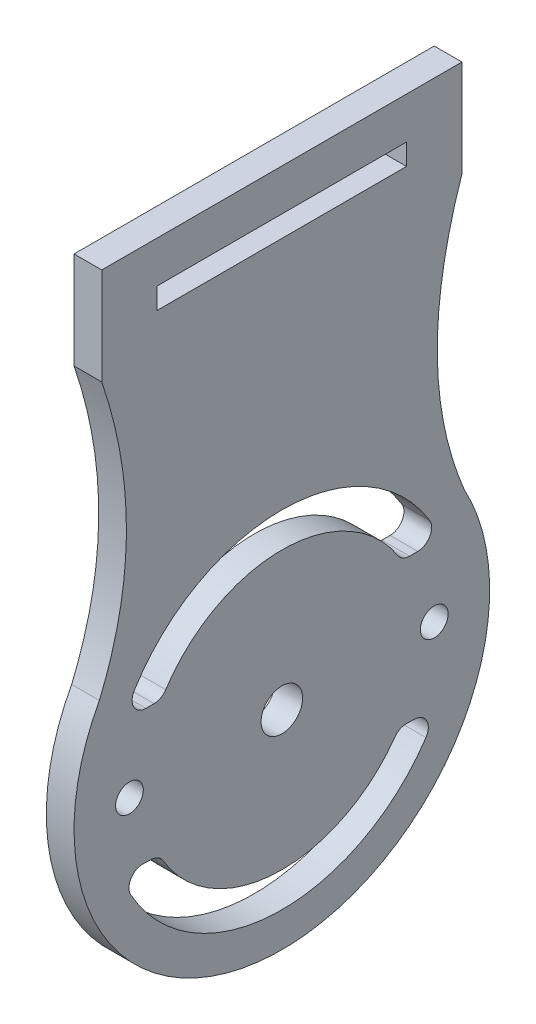
SolidWorks part; units mm, degrees
material "Fibra de Vidro S"
ref_plane "Plano frontal" through (0, 0, 0) normal (0, 0, 1) x (1, 0, 0)
ref_plane "Plano superior" through (0, 0, 0) normal (0, 1, 0) x (1, 0, 0)
ref_plane "Plano direito" through (0, 0, 0) normal (1, 0, 0) x (0, 0, -1)
sketch "Esboço1" plane through (0, 0, 0) normal (1, 0, 0) x (0, 0, -1)
  line L0 (-13, 34) -> (0, 34)
  line L2 (-13, 34) -> (-13, 27)
  line L3 (0, 34) -> (0, -15)
  arc A0 (-13.174, 7.1726) -> (0, -15) centre (0, 0) ccw
  spline S0 degree 2 poles (-13, 27) (-9.3542, 16.24) (-13.174, 7.1726) knots 0 0 0 0.912496 0.912496 0.912496
  dimension "D1" = 30
  dimension "D3" = 34
  dimension "D4" = 7
extrude "Ressalto-extrusão1" add sketch "Esboço1" along normal blind 2
mirror "Espelhar1" about plane through (2, 34, 0) normal (0, 0, 1) of "Ressalto-extrusão1"
sketch "Esboço2" plane through (2, 0, 0) normal (1, 0, 0) x (0, 0, -1)
  line L0 (13, 34) -> (-13, 34) construction
  line L1 (-9, 31) -> (9, 31)
  line L2 (-9, 31) -> (-9, 29.4721)
  line L3 (-9, 29.4721) -> (9, 29.4721)
  line L4 (9, 31) -> (9, 29.4721)
  line L5 (-9, 31) -> (9, 29.4721) construction
  line L6 (-9, 29.4721) -> (9, 31) construction
  line L7 (-9.8107, 5) -> (-9.2195, 5)
  line L8 (9.2195, 5) -> (9.8107, 5)
  line L9 (-9.9967, -4.6168) -> (-9.406, -4.6397)
  line L10 (9.0193, -5.3528) -> (9.61, -5.3757)
  arc A0 (10.6638, 6.5217) -> (-10.6638, 6.5217) centre (0, 0) ccw
  arc A1 (8.3814, 5.4545) -> (-8.3814, 5.4545) centre (0, 0) ccw
  arc A2 (-8.5861, -5.1263) -> (8.1642, -5.7746) centre (0, 0) ccw
  arc A3 (-10.9081, -6.1045) -> (10.4036, -6.9293) centre (0, 0) ccw
  arc A4 (-8.5861, -5.1263) -> (-9.406, -4.6397) centre (-9.4447, -5.639) ccw
  arc A5 (-9.9967, -4.6168) -> (-10.9081, -6.1045) centre (-10.0354, -5.6161) ccw
  arc A6 (10.4036, -6.9293) -> (9.61, -5.3757) centre (9.5713, -6.3749) ccw
  arc A7 (9.0193, -5.3528) -> (8.1642, -5.7746) centre (8.9806, -6.3521) ccw
  arc A8 (9.2195, 5) -> (8.3814, 5.4545) centre (9.2195, 6) cw
  arc A9 (9.8107, 5) -> (10.6638, 6.5217) centre (9.8107, 6) ccw
  arc A10 (-9.2195, 5) -> (-8.3814, 5.4545) centre (-9.2195, 6) ccw
  arc A11 (-9.8107, 5) -> (-10.6638, 6.5217) centre (-9.8107, 6) cw
  circle A12 centre (0, 0) radius 1.5
  circle A13 centre (11, 0) radius 1
  circle A14 centre (-11, 0) radius 1
  point P0 (0, 30.2361)
  point P21 (-11.6412, -4.5532)
  point P26 (8.4604, -5.3312)
  dimension "D3" = 25
  dimension "D4" = 20
  dimension "D7" = 1
  dimension "D8" = 3
  dimension "D9" = 2
  dimension "D11" = 2
  dimension "D1" = 3
  dimension "D2" = 18
  dimension "D5" = 5
  dimension "D6" = 5
  dimension "D10" = 11
  dimension "D12" = 11
extrude "Corte-extrusão1" cut sketch "Esboço2" against normal through all
